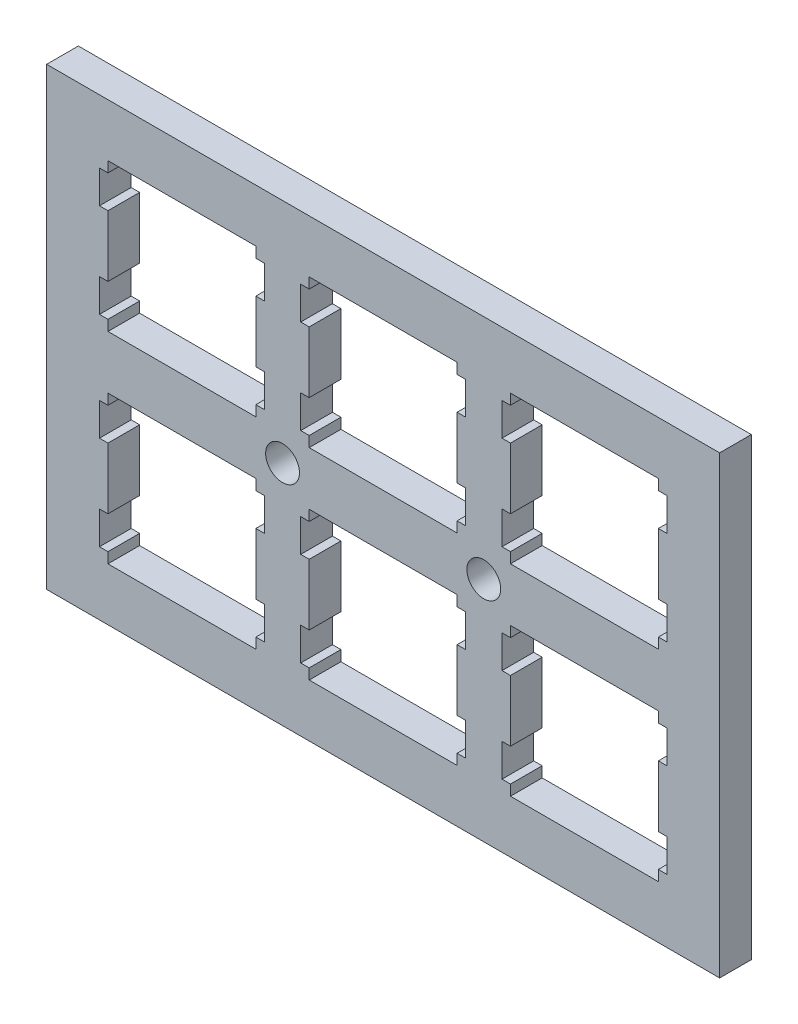
SolidWorks part; units mm, degrees
material "1023 碳钢板 (SS)"
ref_plane "前视基准面" through (0, 0, 0) normal (0, 0, 1) x (1, 0, 0)
ref_plane "上视基准面" through (0, 0, 0) normal (0, 1, 0) x (1, 0, 0)
ref_plane "右视基准面" through (0, 0, 0) normal (1, 0, 0) x (0, 0, -1)
sketch "Model" plane through (0, 0, 0) normal (0, 0, 1) x (1, 0, 0)
  line L0 (43.9194, 18.9186) -> (43.9194, 17.9182)
  line L1 (43.9194, 17.9182) -> (43.1186, 17.9182)
  line L2 (43.1186, 17.9182) -> (43.1186, 14.819)
  line L3 (43.1186, 14.819) -> (43.9194, 14.819)
  line L4 (43.9194, 14.819) -> (43.9194, 9.0188)
  line L5 (43.9194, 9.0188) -> (43.1186, 9.0188)
  line L6 (43.1186, 9.0188) -> (43.1186, 5.9182)
  line L7 (43.1186, 5.9182) -> (43.9194, 5.9182)
  line L8 (43.9194, 5.9182) -> (43.9194, 4.9191)
  line L9 (43.9194, 4.9191) -> (57.9187, 4.9191)
  line L10 (57.9187, 4.9191) -> (57.9187, 5.9182)
  line L11 (57.9187, 5.9182) -> (58.7195, 5.9182)
  line L12 (58.7195, 5.9182) -> (58.7195, 9.0188)
  line L13 (58.7195, 9.0188) -> (57.9187, 9.0188)
  line L14 (57.9187, 9.0188) -> (57.9187, 14.819)
  line L15 (57.9187, 14.819) -> (58.7195, 14.819)
  line L16 (58.7195, 14.819) -> (58.7195, 17.9182)
  line L17 (58.7195, 17.9182) -> (57.9187, 17.9182)
  line L18 (57.9187, 17.9182) -> (57.9187, 18.9186)
  line L19 (57.9187, 18.9186) -> (43.9194, 18.9186)
  line L20 (24.8694, 18.9186) -> (24.8694, 17.9182)
  line L21 (24.8694, 17.9182) -> (24.0687, 17.9182)
  line L22 (24.0687, 17.9182) -> (24.0687, 14.819)
  line L23 (24.0687, 14.819) -> (24.8694, 14.819)
  line L24 (24.8694, 14.819) -> (24.8694, 9.0188)
  line L25 (24.8694, 9.0188) -> (24.0687, 9.0188)
  line L26 (24.0687, 9.0188) -> (24.0687, 5.9182)
  line L27 (24.0687, 5.9182) -> (24.8694, 5.9182)
  line L28 (24.8694, 5.9182) -> (24.8694, 4.9191)
  line L29 (24.8694, 4.9191) -> (38.8687, 4.9191)
  line L30 (38.8687, 4.9191) -> (38.8687, 5.9182)
  line L31 (38.8687, 5.9182) -> (39.6695, 5.9182)
  line L32 (39.6695, 5.9182) -> (39.6695, 9.0188)
  line L33 (39.6695, 9.0188) -> (38.8687, 9.0188)
  line L34 (38.8687, 9.0188) -> (38.8687, 14.819)
  line L35 (38.8687, 14.819) -> (39.6695, 14.819)
  line L36 (39.6695, 14.819) -> (39.6695, 17.9182)
  line L37 (39.6695, 17.9182) -> (38.8687, 17.9182)
  line L38 (38.8687, 17.9182) -> (38.8687, 18.9186)
  line L39 (38.8687, 18.9186) -> (24.8694, 18.9186)
  line L40 (5.8194, 18.9186) -> (5.8194, 17.9182)
  line L41 (5.8194, 17.9182) -> (5.0188, 17.9182)
  line L42 (5.0188, 17.9182) -> (5.0188, 14.819)
  line L43 (5.0188, 14.819) -> (5.8194, 14.819)
  line L44 (5.8194, 14.819) -> (5.8194, 9.0188)
  line L45 (5.8194, 9.0188) -> (5.0188, 9.0188)
  line L46 (5.0188, 9.0188) -> (5.0188, 5.9182)
  line L47 (5.0188, 5.9182) -> (5.8194, 5.9182)
  line L48 (5.8194, 5.9182) -> (5.8194, 4.9191)
  line L49 (5.8194, 4.9191) -> (19.8189, 4.9191)
  line L50 (19.8189, 4.9191) -> (19.8189, 5.9182)
  line L51 (19.8189, 5.9182) -> (20.6195, 5.9182)
  line L52 (20.6195, 5.9182) -> (20.6195, 9.0188)
  line L53 (20.6195, 9.0188) -> (19.8189, 9.0188)
  line L54 (19.8189, 9.0188) -> (19.8189, 14.819)
  line L55 (19.8189, 14.819) -> (20.6195, 14.819)
  line L56 (20.6195, 14.819) -> (20.6195, 17.9182)
  line L57 (20.6195, 17.9182) -> (19.8189, 17.9182)
  line L58 (19.8189, 17.9182) -> (19.8189, 18.9186)
  line L59 (19.8189, 18.9186) -> (5.8194, 18.9186)
  line L60 (43.9194, 37.9685) -> (43.9194, 36.9682)
  line L61 (43.9194, 36.9682) -> (43.1186, 36.9682)
  line L62 (43.1186, 36.9682) -> (43.1186, 33.869)
  line L63 (43.1186, 33.869) -> (43.9194, 33.869)
  line L64 (43.9194, 33.869) -> (43.9194, 28.0688)
  line L65 (43.9194, 28.0688) -> (43.1186, 28.0688)
  line L66 (43.1186, 28.0688) -> (43.1186, 24.9682)
  line L67 (43.1186, 24.9682) -> (43.9194, 24.9682)
  line L68 (43.9194, 24.9682) -> (43.9194, 23.9691)
  line L69 (43.9194, 23.9691) -> (57.9187, 23.9691)
  line L70 (57.9187, 23.9691) -> (57.9187, 24.9682)
  line L71 (57.9187, 24.9682) -> (58.7195, 24.9682)
  line L72 (58.7195, 24.9682) -> (58.7195, 28.0688)
  line L73 (58.7195, 28.0688) -> (57.9187, 28.0688)
  line L74 (57.9187, 28.0688) -> (57.9187, 33.869)
  line L75 (57.9187, 33.869) -> (58.7195, 33.869)
  line L76 (58.7195, 33.869) -> (58.7195, 36.9682)
  line L77 (58.7195, 36.9682) -> (57.9187, 36.9682)
  line L78 (57.9187, 36.9682) -> (57.9187, 37.9685)
  line L79 (57.9187, 37.9685) -> (43.9194, 37.9685)
  line L80 (24.8694, 37.9685) -> (24.8694, 36.9682)
  line L81 (24.8694, 36.9682) -> (24.0687, 36.9682)
  line L82 (24.0687, 36.9682) -> (24.0687, 33.869)
  line L83 (24.0687, 33.869) -> (24.8694, 33.869)
  line L84 (24.8694, 33.869) -> (24.8694, 28.0688)
  line L85 (24.8694, 28.0688) -> (24.0687, 28.0688)
  line L86 (24.0687, 28.0688) -> (24.0687, 24.9682)
  line L87 (24.0687, 24.9682) -> (24.8694, 24.9682)
  line L88 (24.8694, 24.9682) -> (24.8694, 23.9691)
  line L89 (24.8694, 23.9691) -> (38.8687, 23.9691)
  line L90 (38.8687, 23.9691) -> (38.8687, 24.9682)
  line L91 (38.8687, 24.9682) -> (39.6695, 24.9682)
  line L92 (39.6695, 24.9682) -> (39.6695, 28.0688)
  line L93 (39.6695, 28.0688) -> (38.8687, 28.0688)
  line L94 (38.8687, 28.0688) -> (38.8687, 33.869)
  line L95 (38.8687, 33.869) -> (39.6695, 33.869)
  line L96 (39.6695, 33.869) -> (39.6695, 36.9682)
  line L97 (39.6695, 36.9682) -> (38.8687, 36.9682)
  line L98 (38.8687, 36.9682) -> (38.8687, 37.9685)
  line L99 (38.8687, 37.9685) -> (24.8694, 37.9685)
  line L100 (5.8194, 37.9685) -> (5.8194, 36.9682)
  line L101 (5.8194, 36.9682) -> (5.0188, 36.9682)
  line L102 (5.0188, 36.9682) -> (5.0188, 33.869)
  line L103 (5.0188, 33.869) -> (5.8194, 33.869)
  line L104 (5.8194, 33.869) -> (5.8194, 28.0688)
  line L105 (5.8194, 28.0688) -> (5.0188, 28.0688)
  line L106 (5.0188, 28.0688) -> (5.0188, 24.9682)
  line L107 (5.0188, 24.9682) -> (5.8194, 24.9682)
  line L108 (5.8194, 24.9682) -> (5.8194, 23.9691)
  line L109 (5.8194, 23.9691) -> (19.8189, 23.9691)
  line L110 (19.8189, 23.9691) -> (19.8189, 24.9682)
  line L111 (19.8189, 24.9682) -> (20.6195, 24.9682)
  line L112 (20.6195, 24.9682) -> (20.6195, 28.0688)
  line L113 (20.6195, 28.0688) -> (19.8189, 28.0688)
  line L114 (19.8189, 28.0688) -> (19.8189, 33.869)
  line L115 (19.8189, 33.869) -> (20.6195, 33.869)
  line L116 (20.6195, 33.869) -> (20.6195, 36.9682)
  line L117 (20.6195, 36.9682) -> (19.8189, 36.9682)
  line L118 (19.8189, 36.9682) -> (19.8189, 37.9685)
  line L119 (19.8189, 37.9685) -> (5.8194, 37.9685)
  line L120 (0.0188, 42.9685) -> (63.7195, 42.9685)
  line L121 (63.7195, 42.9685) -> (63.7195, -0.0809)
  line L122 (63.7195, -0.0809) -> (0.0188, -0.0809)
  line L123 (0.0188, -0.0809) -> (0.0188, 42.9685)
  circle A0 centre (22.3442, 21.4432) radius 1.6
  circle A1 centre (41.3941, 21.4432) radius 1.6
extrude "凸台-拉伸1" add sketch "Model" along normal blind 3
